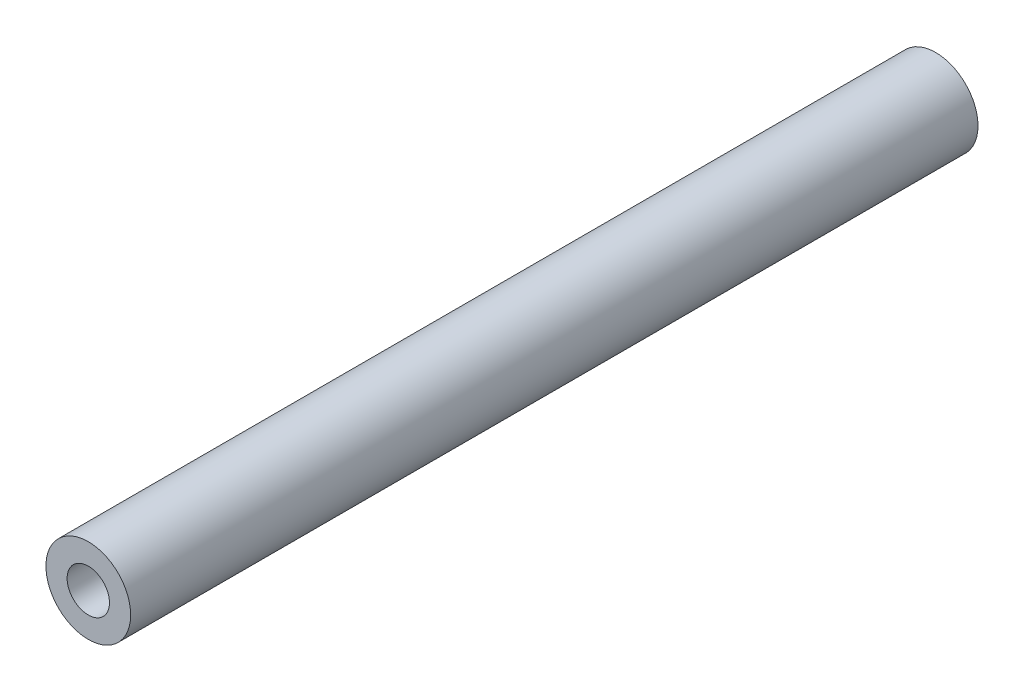
SolidWorks part; units mm, degrees
material "6061 合金"
ref_plane "前视基准面" through (0, 0, 0) normal (0, 0, 1) x (1, 0, 0)
ref_plane "上视基准面" through (0, 0, 0) normal (0, 1, 0) x (1, 0, 0)
ref_plane "右视基准面" through (0, 0, 0) normal (1, 0, 0) x (0, 0, -1)
sketch "草图1" plane through (0, 0, 0) normal (0, 0, 1) x (1, 0, 0)
  circle A1 centre (0, 0) radius 2.5
  dimension "D1" = 5
extrude "凸台-拉伸1" add sketch "草图1" along normal blind 50
hole_wizard "M3 螺纹孔1" positions "草图2" profile "草图3" tap size "M3" standard "GB" end condition through all
sketch "草图2" plane through (0, 0, 50) normal (0, 0, 1) x (1, 0, 0)
  point P0 (0, 0)
sketch "草图3" plane through (0, 0, 50) normal (1, 0, 0) x (0, -1, 0)
  line L0 (0, 0) -> (0, 50)
  line L1 (0, 50) -> (1.25, 50)
  line L2 (1.25, 50) -> (1.25, 0)
  line L5 (1.25, 0) -> (0, 0)
  line L11 (0, -6.35) -> (0, 107.95) construction
  dimension "通孔螺纹孔钻头直径" = 2.5
  dimension "通孔螺纹孔钻头深度" = 50
cosmetic thread "孔螺蚊线1"
